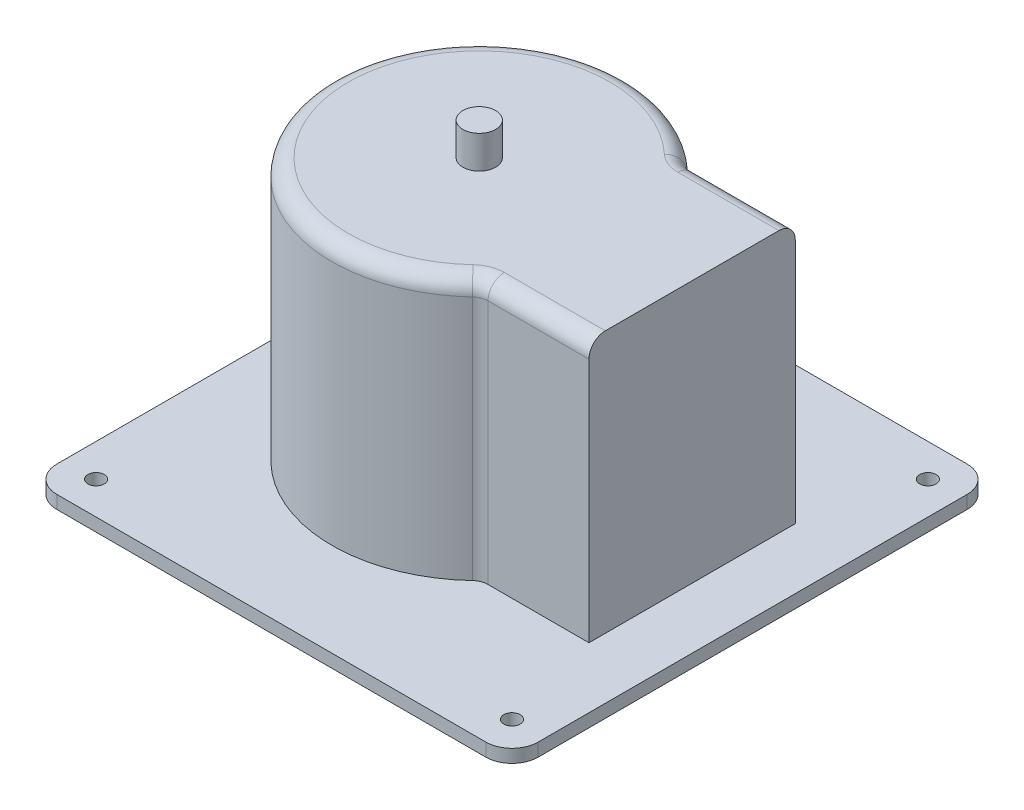
SolidWorks part; units mm, degrees
ref_plane "Front Plane" through (0, 0, 0) normal (0, 0, 1) x (1, 0, 0)
ref_plane "Top Plane" through (0, 0, 0) normal (0, 1, 0) x (1, 0, 0)
ref_plane "Right Plane" through (0, 0, 0) normal (1, 0, 0) x (0, 0, -1)
sketch "Sketch1" plane through (0, 0, 0) normal (0, 1, 0) x (1, 0, 0)
  circle A0 centre (0, 0) radius 45
  dimension "D1" = 90
extrude "Boss-Extrude1" add sketch "Sketch1" along normal blind 80
ref_plane "Plane1" through (65, 0, 0) normal (1, 0, 0) x (0, 0, -1)
sketch "Sketch2" plane through (65, 0, 0) normal (1, 0, 0) x (0, 0, -1)
  line L5 (45, 80) -> (-45, 80) construction
  line L6 (-31.5, 80) -> (31.5, 80)
  line L7 (-31.5, 80) -> (-31.5, 0)
  line L8 (-31.5, 0) -> (31.5, 0)
  line L9 (31.5, 80) -> (31.5, 0)
  line L10 (-45, 0) -> (45, 0) construction
  point P6 (0, 0)
  dimension "D1" = 63
extrude "Boss-Extrude2" add sketch "Sketch2" against normal up to surface (32.8636 mm away)
fillet "Fillet1" radius 5 5 edges at (-45, 80, 0) (32.1364, 40, 31.5) (32.1364, 40, -31.5) (48.5682, 80, -31.5) (48.5682, 80, 31.5)
sketch "Sketch3" plane through (0, 80, 0) normal (0, 1, 0) x (1, 0, 0)
  circle A0 centre (0, 0) radius 5
  dimension "D1" = 10
extrude "Boss-Extrude3" add sketch "Sketch3" along normal blind 10
sketch "Sketch4" plane through (0, 0, 0) normal (0, -1, 0) x (1, 0, 0)
  line L0 (-45, 0) -> (65, 0) construction
  line L1 (-63.5, 73.5) -> (83.5, 73.5)
  line L2 (-63.5, 73.5) -> (-63.5, -73.5)
  line L3 (-63.5, -73.5) -> (83.5, -73.5)
  line L4 (83.5, 73.5) -> (83.5, -73.5)
  line L5 (65, 31.5) -> (65, -31.5) construction
  arc A0 (30.7551, 32.85) -> (30.7551, -32.85) centre (0, 0) ccw construction
  point P11 (10, 0)
  point P12 (10, 73.5)
  point P13 (83.5, 0)
  dimension "D1" = 147
  dimension "D2" = 147
extrude "Boss-Extrude4" add sketch "Sketch4" along normal blind 4
sketch "Sketch5" plane through (0, 0, 0) normal (0, 1, 0) x (1, 0, 0)
  line L0 (-63.5, 73.5) -> (83.5, 73.5) construction
  line L1 (-63.5, -73.5) -> (-63.5, 73.5) construction
  line L2 (83.5, 73.5) -> (83.5, -73.5) construction
  line L3 (83.5, -73.5) -> (-63.5, -73.5) construction
  circle A0 centre (-53.5, 63.5) radius 2.5
  circle A1 centre (73.5, 63.5) radius 2.5
  circle A2 centre (-53.5, -63.5) radius 2.5
  circle A3 centre (73.5, -63.5) radius 2.5
  point P12 (0, 0)
  point P15 (0, 0)
  point P18 (0, 0)
  point P19 (0, 0)
  dimension "D1" = 5
  dimension "D2" = 10
  dimension "D3" = 10
  dimension "D4" = 10
  dimension "D5" = 10
extrude "Cut-Extrude1" cut sketch "Sketch5" against normal through all
fillet "Fillet2" radius 8 4 edges at (-63.5, -2, 73.5) (83.5, -2, 73.5) (83.5, -2, -73.5) (-63.5, -2, -73.5)
